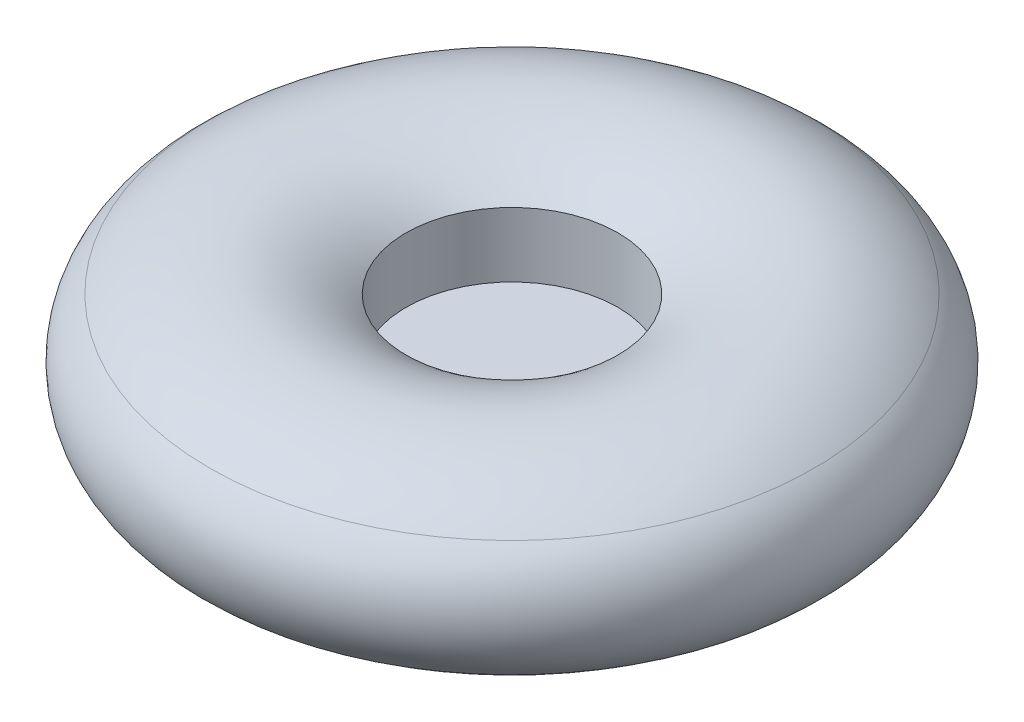
SolidWorks part; units mm, degrees
ref_plane "Front" through (0, 0, 0) normal (0, 0, 1) x (1, 0, 0)
ref_plane "Top" through (0, 0, 0) normal (0, 1, 0) x (1, 0, 0)
ref_plane "Right" through (0, 0, 0) normal (1, 0, 0) x (0, 0, -1)
sketch "Sketch1" plane through (0, 0, 0) normal (0, 0, 1) x (1, 0, 0)
  line L0 (0, 0) -> (0, 90.2141) construction
  line L1 (0, 0) -> (0, 1.9281)
  line L2 (0, 1.9281) -> (57.15, 1.9281)
  line L3 (57.15, 36.7501) -> (57.15, 1.9281)
  line L4 (57.15, -2.8344) -> (0, -2.8344)
  line L5 (0, -2.8344) -> (0, 0)
  line L6 (177.8, 52.307) -> (177.8, -31.5247) construction
  line L7 (57.15, -25.9519) -> (57.15, -2.8344)
  arc A3 (57.15, 36.7501) -> (162.9552, 36.7501) centre (110.0526, -27.8272) cw
  arc A4 (162.9552, 36.7501) -> (162.9552, -25.9519) centre (137.2721, 5.3991) cw
  arc A5 (162.9552, -25.9519) -> (57.15, -25.9519) centre (110.0526, 38.6255) cw
  dimension "D1" = 177.8
  dimension "D2" = 4.7625
  dimension "D3" = 114.3
revolve "Revolve1" add sketch "Sketch1" angle 360 about L0
